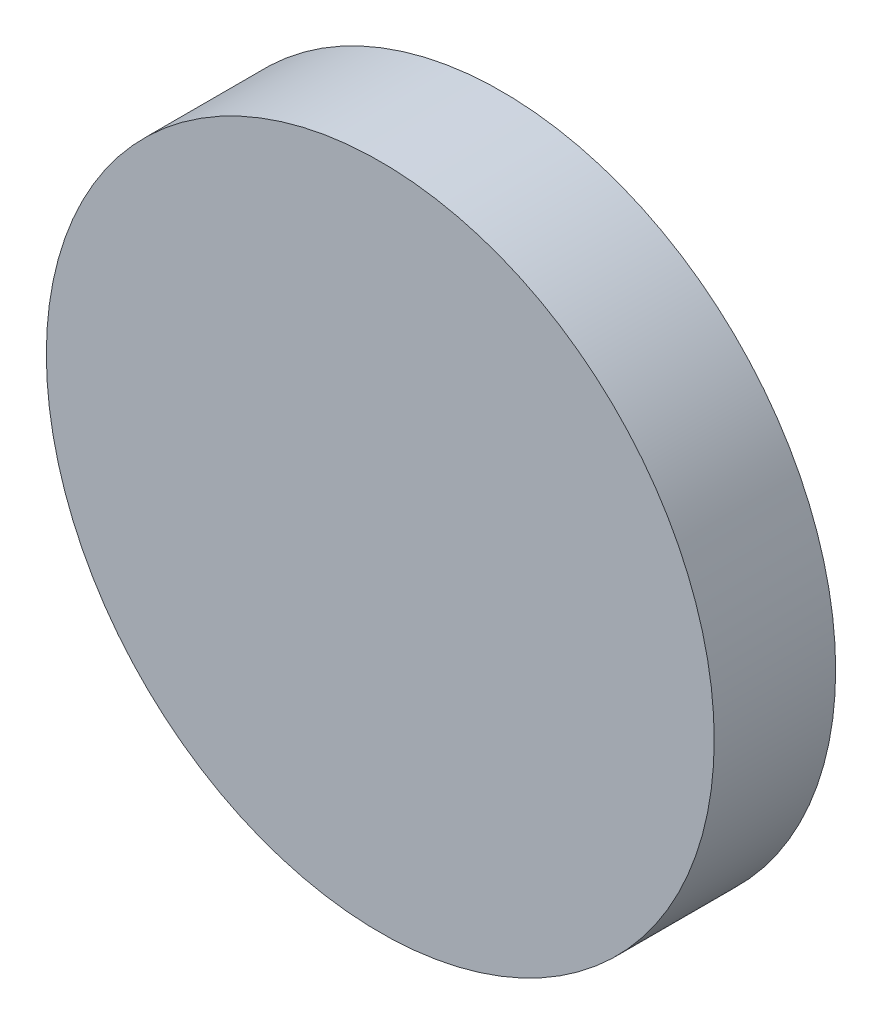
SolidWorks part; units mm, degrees
ref_plane "Front Plane" through (0, 0, 0) normal (0, 0, 1) x (1, 0, 0)
ref_plane "Top Plane" through (0, 0, 0) normal (0, 1, 0) x (1, 0, 0)
ref_plane "Right Plane" through (0, 0, 0) normal (1, 0, 0) x (0, 0, -1)
sketch "Sketch1" plane through (0, 0, 0) normal (0, 0, 1) x (1, 0, 0)
  circle A0 centre (0, 0) radius 34.925
  dimension "D1" = 69.85
extrude "Boss-Extrude1" add sketch "Sketch1" along normal blind 12.7
